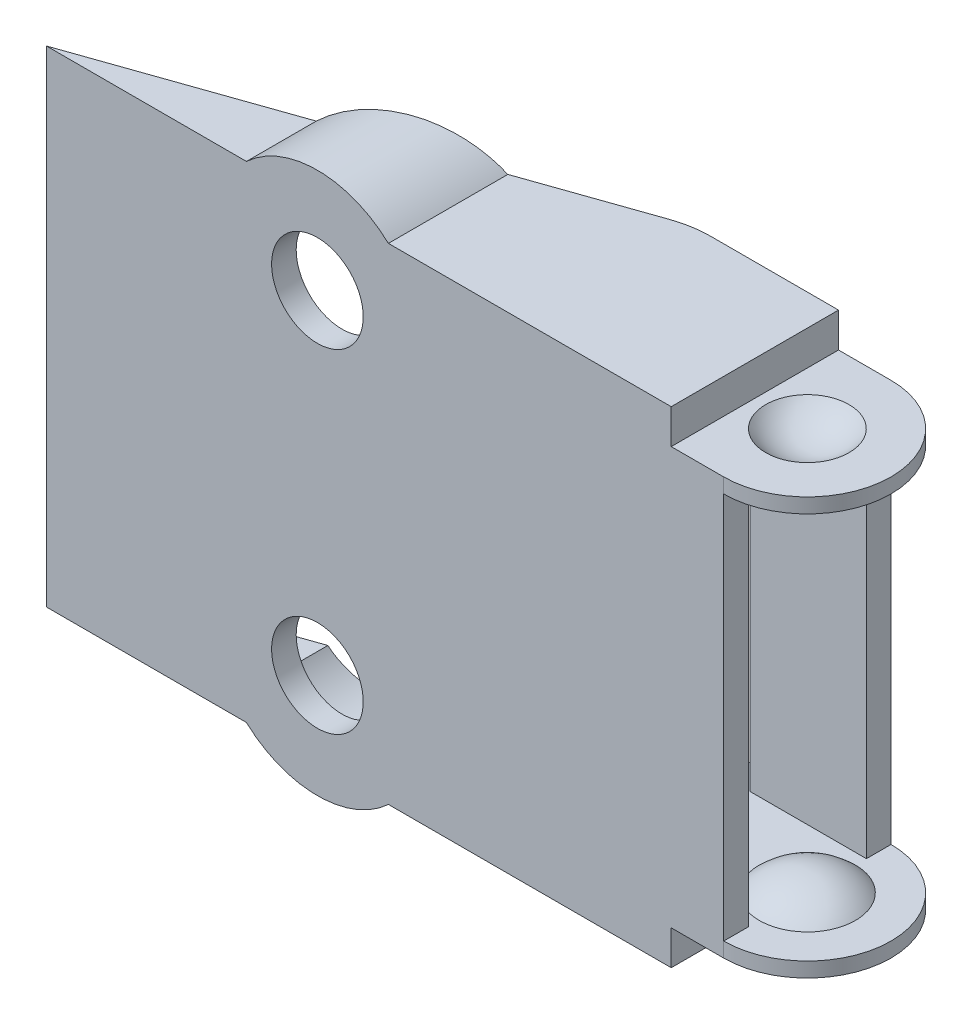
SolidWorks part; units mm, degrees
ref_plane "Front Plane" through (0, 0, 0) normal (0, 0, 1) x (1, 0, 0)
ref_plane "Top Plane" through (0, 0, 0) normal (0, 1, 0) x (1, 0, 0)
ref_plane "Right Plane" through (0, 0, 0) normal (1, 0, 0) x (0, 0, -1)
sketch "Sketch1" plane through (0, 0, 0) normal (0, 0, 1) x (1, 0, 0)
  line L0 (-6.35, 0) -> (6.35, 0)
  line L1 (6.35, 0) -> (6.35, -9.525)
  line L2 (6.35, -9.525) -> (-6.35, -9.525)
  line L3 (-6.35, -9.525) -> (-6.35, 0)
  point P3 (0, -9.525)
  point P6 (0, 0)
  dimension "D1" = 9.525
  dimension "D2" = 12.7
sketch "Sketch3" plane through (0, 0, 0) normal (0, 1, 0) x (1, 0, 0)
  line L0 (6.35, 0) -> (-6.35, 0) construction
  line L1 (-6.35, 0) -> (6.35, 0) construction
  circle A0 centre (-6.35, 3.175) radius 3.175
  circle A1 centre (6.35, 3.175) radius 3.175
  dimension "D1" = 6.35
sketch "Sketch6" plane through (0, 0, 0) normal (0, 1, 0) x (1, 0, 0)
  line L0 (-6.35, 0) -> (-8.1461, 0) construction
  line L1 (-8.1461, 0) -> (-9.0713, 1.5395) construction
  line L2 (3.1496, 3.175) -> (3.1496, 8.2738)
  line L3 (4.5243, 0) -> (3.6069, 1.5264) construction
  line L4 (6.35, 0) -> (-6.35, 0) construction
  line L5 (-6.35, 0) -> (4.5243, 0) construction
  line L6 (-8.1461, 0) -> (-6.9899, -1.9238) construction
  line L7 (-6.9899, -1.9238) -> (3.1496, -1.9238)
  line L8 (5.5675, -1.7359) -> (4.5243, 0) construction
  line L9 (3.1496, 3.175) -> (3.1496, -1.9238)
  line L10 (-8.5951, 5.4201) -> (-5.7413, 8.2738)
  line L11 (-5.7413, 8.2738) -> (3.1496, 8.2738)
  line L12 (-9.525, 3.175) -> (-9.525, -1.9238)
  line L13 (-9.525, -1.9238) -> (-6.9899, -1.9238)
  line L14 (-6.9587, -1.9238) -> (-5.7413, 8.2738) construction
  circle A0 centre (-6.35, 3.175) radius 3.175 construction
  circle A1 centre (6.35, 3.175) radius 3.175 construction
  arc A2 (-8.5951, 5.4201) -> (-9.525, 3.175) centre (-6.35, 3.175) ccw
  arc A4 (3.1496, 3.175) -> (3.6069, 1.5264) centre (6.35, 3.175) ccw construction
  point P21 (-6.35, 3.175)
  dimension "D2" = 0.0254
  dimension "D4" = 45
extrude "Boss-Extrude2" add sketch "Sketch6" along normal blind 2.1082
sketch "Sketch7" plane through (0, 0, 0) normal (0, -1, 0) x (1, 0, 0)
  line L0 (-9.525, 1.9238) -> (3.1496, 1.9238) construction
  line L1 (-2.0506, 1.9238) -> (-2.0506, 0.4238)
  line L6 (6.35, -8.2738) -> (-4.018, -8.2738)
  line L7 (3.1496, -8.2738) -> (-5.7413, -8.2738) construction
  line L8 (3.1496, -8.2738) -> (-5.7413, -8.2738) construction
  line L9 (6.35, 1.9238) -> (-2.0506, 1.9238)
  arc A1 (6.35, -8.2738) -> (6.35, 1.9238) centre (6.35, -3.175) ccw
  arc A2 (-9.525, -3.175) -> (-8.5951, -5.4201) centre (-6.35, -3.175) ccw construction
  arc A3 (-9.525, -3.175) -> (-8.5951, -5.4201) centre (-6.35, -3.175) ccw
  circle A4 centre (-6.35, -3.175) radius 5.0988 construction
  arc A5 (-4.018, -8.2738) -> (-2.0506, 0.4238) centre (-6.35, -3.175) ccw
  dimension "D2" = 0.508
  dimension "D1" = 1.5
extrude "Boss-Extrude3" add sketch "Sketch7" along normal blind 0.9
ref_plane "Plane1" through (0, 0, -3.175) normal (0, 0, 1) x (1, 0, 0)
sketch "Sketch11" plane through (0, 0, -3.175) normal (0, 0, 1) x (1, 0, 0)
  line L1 (9.525, 0) -> (3.175, 0) construction
  line L2 (8.89, 0) -> (9.5454, 0.781) construction
  line L3 (6.35, -0.9) -> (9.2786, -0.9)
  line L4 (6.35, -0.9) -> (11.4488, -0.9) construction
  line L6 (6.35, -0.9) -> (6.35, -2.0836)
  arc A0 (3.81, 0) -> (8.89, 0) centre (6.35, 2.1313) ccw construction
  arc A3 (6.35, -2.0836) -> (9.2786, -0.9) centre (6.35, 2.1313) ccw
  dimension "D1" = 50
  dimension "D2" = 2.54
  dimension "D3" = 0.8992
revolve "Revolve4" add sketch "Sketch11" angle 360 about L6
sketch "Sketch12" plane through (0, 0, -3.175) normal (0, 0, 1) x (1, 0, 0)
  line L1 (9.525, 0) -> (3.175, 0) construction
  line L2 (8.89, 0) -> (6.35, 0)
  line L3 (6.35, 0) -> (6.35, -1.1844)
  arc A0 (3.81, 0) -> (8.89, 0) centre (6.35, 2.1313) ccw construction
  arc A1 (6.35, -1.1844) -> (8.89, 0) centre (6.35, 2.1313) ccw
revolve "Cut-Revolve1" cut sketch "Sketch12" angle 360 about L3
sketch "Sketch13" plane through (0, 0, 0) normal (0, -1, 0) x (1, 0, 0)
  line L1 (6.35, 1.9238) -> (-2.0506, 1.9238) construction
  line L2 (-2.0506, 0.4238) -> (6.35, 0.4238)
  line L3 (-2.0506, 0.4238) -> (-2.0506, 1.9238)
  line L4 (-2.0506, 1.9238) -> (6.35, 1.9238)
  line L5 (6.35, 0.4238) -> (6.35, 1.9238)
  line L6 (-2.0506, 0.4238) -> (6.35, 1.9238) construction
  line L8 (-2.0506, 1.9238) -> (6.35, 0.4238) construction
  arc A0 (-4.018, -8.2738) -> (-2.0506, 0.4238) centre (-6.35, -3.175) ccw construction
  point P0 (2.1497, 1.1738)
extrude "Boss-Extrude4" add sketch "Sketch13" along normal blind 12.7
sketch "Sketch16" plane through (0, -0.9, 0) normal (0, -1, 0) x (1, 0, 0)
  line L0 (-4.018, -8.2738) -> (6.35, -8.2738) construction
  line L1 (6.35, -8.2738) -> (-0.7432, -8.2738)
  line L2 (6.35, -8.2738) -> (6.35, -6.7738)
  line L3 (6.35, -6.7738) -> (-0.7432, -6.7738)
  line L4 (-0.7432, -8.2738) -> (-0.7432, -6.7738)
  line L5 (6.35, 0.4238) -> (6.35, 1.9238) construction
  line L6 (-0.7432, -6.7738) -> (-0.7432, -3.175) construction
  line L7 (-0.7432, -3.175) -> (-9.525, -3.175) construction
  arc A0 (-4.018, -8.2738) -> (-2.0506, 0.4238) centre (-6.35, -3.175) ccw construction
  arc A1 (-4.018, -8.2738) -> (-2.0506, 0.4238) centre (-6.35, -3.175) ccw construction
extrude "Boss-Extrude5" add sketch "Sketch16" along normal up to vertex (11.8 mm away) up to point (6.35, -12.7, 0.4238)
mirror "Mirror1" about plane through (6.35, -12.7, 1.9238) normal (0, 1, 0) of bodies 117 110 114
sketch "Sketch17" plane through (0, -27.5082, 0) normal (0, -1, 0) x (1, 0, 0)
  line L0 (-5.7413, -8.2738) -> (-34.925, 1.9238)
  line L1 (-34.925, 1.9238) -> (-9.525, 1.9238)
  line L2 (-5.7413, -8.2738) -> (-8.5951, -5.4201) construction
  line L3 (-9.525, -3.175) -> (-9.525, 1.9238) construction
  line L4 (-5.7413, -8.2738) -> (-8.5951, -5.4201)
  line L5 (-9.525, -3.175) -> (-9.525, 1.9238)
  arc A0 (-9.525, -3.175) -> (-8.5951, -5.4201) centre (-6.35, -3.175) ccw construction
  arc A1 (-9.525, -3.175) -> (-8.5951, -5.4201) centre (-6.35, -3.175) ccw
  dimension "D1" = 25.4
extrude "Boss-Extrude6" add sketch "Sketch17" against normal up to surface (2.1082 mm away) up to face at (-6.5126, -25.4, -3.5089)
sketch "Sketch18" plane through (-2.0506, 0, 0) normal (-1, 0, 0) x (0, 0, 1)
  line L6 (1.9238, 0) -> (0.4238, 0)
  line L7 (0.4238, 0) -> (0.4238, -0.9)
  line L8 (0.4238, -0.9) -> (0.4238, -24.5)
  line L9 (0.4238, -24.5) -> (0.4238, -25.4)
  line L10 (0.4238, -25.4) -> (1.9238, -25.4)
  line L11 (1.9238, -25.4) -> (1.9238, 0)
  line L12 (1.9238, 0) -> (0.4238, 0)
  line L13 (0.4238, 0) -> (0.4238, -0.9)
  line L14 (0.4238, -0.9) -> (0.4238, -24.5)
  line L15 (0.4238, -24.5) -> (0.4238, -25.4)
  line L16 (0.4238, -25.4) -> (1.9238, -25.4)
  line L17 (1.9238, -25.4) -> (1.9238, 0)
  dimension "D1" = 0
extrude "Boss-Extrude7" add sketch "Sketch18" along normal up to surface (28.5817 mm away)
sketch "Sketch19" plane through (0, 2.1082, 0) normal (0, 1, 0) x (1, 0, 0)
  line L0 (-30.6323, -0.4238) -> (-2.0506, -0.4238) construction
  line L1 (-4.018, 8.2738) -> (-5.7413, 8.2738) construction
  line L2 (-5.7413, 8.2738) -> (-30.6323, -0.4238) construction
  line L3 (-34.925, -1.9238) -> (-9.525, -1.9238) construction
  line L4 (-9.525, -1.9238) -> (-9.525, -0.4238) construction
  line L5 (-9.525, -0.4238) -> (-30.6323, -0.4238) construction
  line L6 (-30.6323, -0.4238) -> (-34.925, -1.9238) construction
  line L7 (-30.6323, -0.4238) -> (-2.0506, -0.4238)
  line L8 (-4.018, 8.2738) -> (-5.7413, 8.2738)
  line L9 (-5.7413, 8.2738) -> (-30.6323, -0.4238)
  line L10 (-34.925, -1.9238) -> (-9.525, -1.9238)
  line L11 (-9.525, -1.9238) -> (-9.525, -0.4238)
  line L12 (-9.525, -0.4238) -> (-30.6323, -0.4238)
  line L13 (-30.6323, -0.4238) -> (-34.925, -1.9238)
  line L14 (-9.525, 3.175) -> (-9.525, -1.9238) construction
  line L15 (-5.7413, 8.2738) -> (-8.5951, 5.4201) construction
  line L16 (-9.525, 3.175) -> (-9.525, -1.9238)
  line L17 (-5.7413, 8.2738) -> (-8.5951, 5.4201)
  arc A0 (-2.0506, -0.4238) -> (-4.018, 8.2738) centre (-6.35, 3.175) ccw construction
  arc A1 (-2.0506, -0.4238) -> (-4.018, 8.2738) centre (-6.35, 3.175) ccw
  arc A2 (-8.5951, 5.4201) -> (-9.525, 3.175) centre (-6.35, 3.175) ccw construction
  arc A3 (-8.5951, 5.4201) -> (-9.525, 3.175) centre (-6.35, 3.175) ccw
  arc M1 (-8.5951, 5.4201) -> (-9.525, 3.175) centre (-6.35, 3.175) ccw
  line M2 (-9.525, 3.175) -> (-9.525, -1.9238)
  line M6 (-5.7413, 8.2738) -> (-8.5951, 5.4201)
extrude "Boss-Extrude8" add sketch "Sketch19" against normal up to surface (2.1082 mm away) contours L9 L7 M6 M2 M1 | L7 L13 L10 M2 up to face at (-6.6334, 0, -4.7894)
fillet "Fillet1" radius 6.35 2 edges at (-5.7413, 1.0541, -8.2738) (-5.7413, -26.4541, -8.2738)
sketch "Sketch20" plane through (0, 0, 0.4238) normal (0, 0, -1) x (-1, 0, 0)
  line L0 (18.415, -20.066) -> (18.415, -5.334) construction
  line L1 (30.6323, 0) -> (30.6323, -25.4) construction
  line L2 (34.925, 2.1082) -> (34.925, -27.5082) construction
  circle A0 centre (18.415, -22.86) radius 2.794
  circle A1 centre (18.415, -2.54) radius 2.794
  point P6 (18.415, -12.7)
  point P9 (30.6323, -12.7)
  dimension "D1" = 14.732
  dimension "D2" = 5.588
  dimension "D3" = 5.588
  dimension "D4" = 16.51
extrude "Cut-Extrude1" cut sketch "Sketch20" against normal through all
sketch "Sketch21" plane through (0, 0, 0.4238) normal (0, 0, -1) x (-1, 0, 0)
  circle A0 centre (18.415, -22.86) radius 4.572
  circle A1 centre (18.415, -2.54) radius 4.572
  dimension "D1" = 9.144
extrude "Cut-Extrude2" cut sketch "Sketch21" along normal through all
sketch "Sketch22" plane through (0, 0, 1.9238) normal (0, 0, 1) x (1, 0, 0)
  line L0 (-34.925, -27.5082) -> (-6.7585, -27.5082) construction
  line L1 (-6.7585, 2.1082) -> (-34.925, 2.1082) construction
  line L2 (-34.925, -27.5082) -> (-6.7585, -27.5082)
  line L3 (-6.7585, 2.1082) -> (-34.925, 2.1082)
  circle A0 centre (-18.415, -22.86) radius 6.35
  circle A1 centre (-18.415, -2.54) radius 6.35
  dimension "D1" = 12.7
extrude "Boss-Extrude9" add sketch "Sketch22" against normal up to surface (4.2573 mm away) contours L2 A0 | L3 A1
